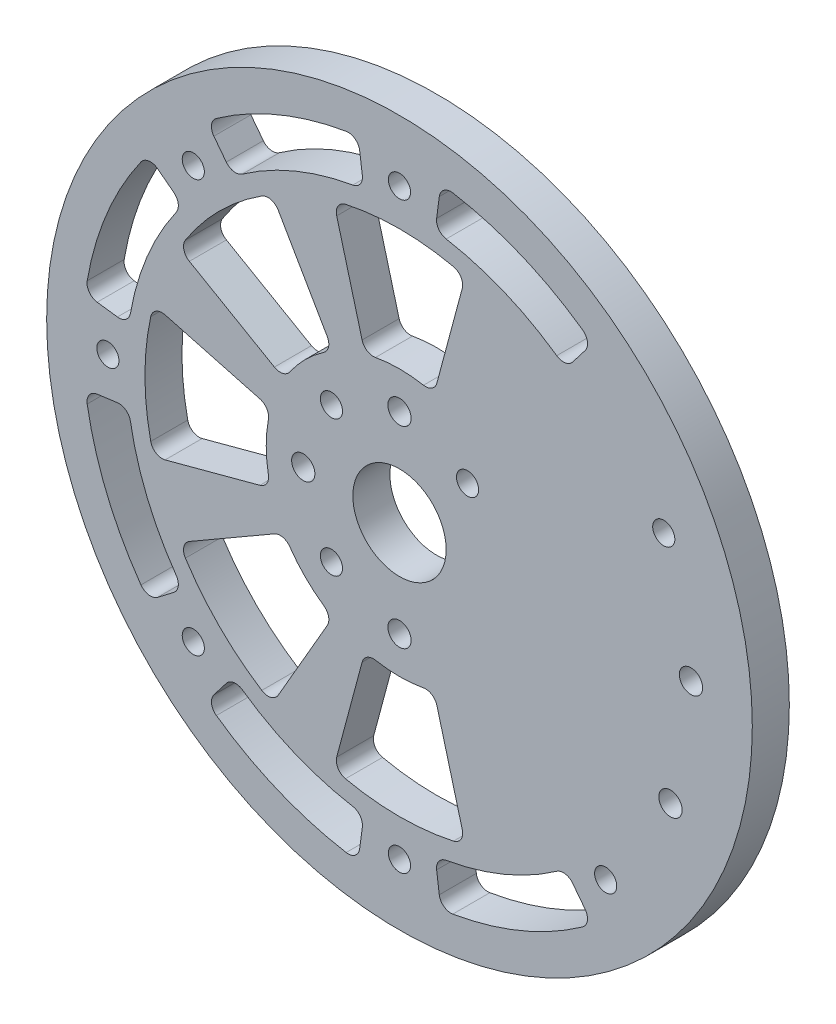
SolidWorks part; units mm, degrees
material "Balsa"
ref_plane "Front Plane" through (0, 0, 0) normal (0, 0, 1) x (1, 0, 0)
ref_plane "Top Plane" through (0, 0, 0) normal (0, 1, 0) x (1, 0, 0)
ref_plane "Right Plane" through (0, 0, 0) normal (1, 0, 0) x (0, 0, -1)
sketch "Sketch1" plane through (0, 0, 0) normal (0, 0, 1) x (1, 0, 0)
  line L0 (45.3154, 21.1309) -> (0, 0) construction
  line L1 (0, 0) -> (35.3553, -35.3553) construction
  line L2 (49.9788, 1.4542) -> (0, 0) construction
  line L3 (0, 0) -> (46.4674, -18.4603) construction
  circle A0 centre (45.3154, 21.1309) radius 1.8986
  circle A1 centre (49.9788, 1.4542) radius 1.9939
  circle A2 centre (0, 0) radius 60.5
  circle A3 centre (0, 0) radius 8
  circle A4 centre (0, 0) radius 16.5 construction
  circle A5 centre (46.4674, -18.4603) radius 1.9939
  circle A6 centre (0, 0) radius 50 construction
  circle A27 centre (0, -16.5) radius 1.9939
  circle A28 centre (11.6673, -11.6673) radius 1.8986 construction
  circle A30 centre (0, -50) radius 1.8986
  circle A31 centre (-16.5, 0) radius 1.9939
  circle A32 centre (-11.6673, -11.6673) radius 1.8986
  circle A33 centre (0, 16.5) radius 1.9939
  circle A34 centre (-11.6673, 11.6673) radius 1.8986
  circle A35 centre (16.5, 0) radius 1.9939 construction
  circle A36 centre (11.6673, 11.6673) radius 1.8986
  circle A38 centre (-35.3553, -35.3553) radius 1.8986
  circle A40 centre (-50, 0) radius 1.8986
  circle A42 centre (-35.3553, 35.3553) radius 1.8986
  circle A44 centre (0, 50) radius 1.8986
  circle A46 centre (35.3553, 35.3553) radius 1.8986 construction
  circle A48 centre (50, 0) radius 1.8986 construction
  circle A50 centre (35.3553, -35.3553) radius 1.8986
  dimension "D1" = 121
  dimension "D4" = 70
  dimension "D6" = 100
  dimension "D7" = 23.333
  dimension "D8" = 33
  dimension "D9" = 3.7973
  dimension "D10" = 3.9878
  dimension "D15" = 3.7973
  dimension "D17" = 3.9878
  dimension "D18" = 3.7973
  dimension "D3" = 16
  dimension "D11" = 3.9878
  dimension "D5" = 23.333
  dimension "D19" = 45
  dimension "D20" = 4
  dimension "D21" = 8
extrude "Boss-Extrude1" add sketch "Sketch1" along normal blind 6.35
sketch "Sketch2" plane through (0, 0, 6.35) normal (0, 0, 1) x (1, 0, 0)
  line L0 (0, 0) -> (-83.0843, 0) construction
  line L1 (-22.0714, 5.914) -> (-42.1627, 11.2975)
  line L2 (-22.0714, -5.914) -> (-42.1627, -11.2975)
  arc A0 (-42.1627, -11.2975) -> (-42.1627, 11.2975) centre (0, 0) cw
  arc A1 (-22.0714, -5.914) -> (-22.0714, 5.914) centre (0, 0) cw
  circle A2 centre (-16.5, 0) radius 1.9939 construction
  circle A3 centre (-50, 0) radius 1.8987 construction
  point P7 (-22.85, 0)
  point P10 (-43.65, 0)
  dimension "D2" = 6.35
  dimension "D3" = 6.35
  dimension "D1" = 30
extrude "Cut-Extrude1" cut sketch "Sketch2" against normal through all
fillet "Fillet1" radius 2 4 edges at (-42.1627, -11.2975, 3.175) (-22.0714, -5.914, 3.175) (-22.0714, 5.914, 3.175) (-42.1627, 11.2975, 3.175)
pattern_circular "CirPattern1" count 8 over 360 about axis through (0, 0, 0) along (0, 0, 1) skipping 3, 4, 5 of "Fillet1", "Cut-Extrude1"
sketch "Sketch3" plane through (0, 0, 6.35) normal (0, 0, 1) x (1, 0, 0)
  line L0 (-83.2273, 0) -> (0, 0) construction
  line L1 (0, 0) -> (-85.2421, 35.3084) construction
  line L2 (-43.0989, 33.071) -> (-37.1488, 28.5053)
  line L3 (-46.4244, 6.1119) -> (-53.8602, 7.0908)
  arc A0 (-53.8602, 7.0908) -> (-43.0989, 33.071) centre (0, 0) cw
  arc A1 (-46.4244, 6.1119) -> (-37.1488, 28.5053) centre (0, 0) cw
  circle A2 centre (-50, 0) radius 1.8987 construction
  circle A3 centre (-50, 0) radius 1.8986 construction
  circle A4 centre (0, 0) radius 60.5 construction
  arc A5 (-42.6565, 9.2598) -> (-42.6565, -9.2598) centre (0, 0) ccw construction
  point P12 (-43.2607, 17.9192)
  dimension "D3" = 6.175
  dimension "D4" = 3.175
  dimension "D1" = 22.5
  dimension "D2" = 30
extrude "Cut-Extrude2" cut sketch "Sketch3" against normal through all
fillet "Fillet2" radius 2 4 edges at (-53.8602, 7.0908, 3.175) (-46.4244, 6.1119, 3.175) (-37.1488, 28.5053, 3.175) (-43.0989, 33.071, 3.175)
pattern_circular "CirPattern3" count 8 over 360 about axis through (0, 0, 0) along (0, 0, 1) skipping 3, 4 of "Cut-Extrude2", "Fillet2"
sketch "Sketch4" plane through (0, 0, 0) normal (0, 0, -1) x (-1, 0, 0)
  circle A0 centre (0, 50) radius 1.8986 construction
  circle A1 centre (35.3553, 35.3553) radius 1.8987 construction
  circle A2 centre (50, 0) radius 1.8987 construction
  circle A3 centre (35.3553, -35.3553) radius 1.8987 construction
  circle A4 centre (0, -50) radius 1.8986 construction
  circle A5 centre (-35.3553, -35.3553) radius 1.8987 construction
  circle A6 centre (-45.3154, 21.1309) radius 1.8987 construction
  circle A7 centre (0, 50) radius 1.8986
  circle A8 centre (35.3553, 35.3553) radius 1.8986
  circle A9 centre (50, 0) radius 1.8986
  circle A10 centre (35.3553, -35.3553) radius 1.8986
  circle A11 centre (0, -50) radius 1.8986
  circle A12 centre (-35.3553, -35.3553) radius 1.8986
  circle A13 centre (-45.3154, 21.1309) radius 1.8986
  circle A14 centre (0, 50) radius 4.7625
  circle A15 centre (35.3553, 35.3553) radius 4.7625
  circle A16 centre (50, 0) radius 4.7625
  circle A17 centre (35.3553, -35.3553) radius 4.7625
  circle A18 centre (0, -50) radius 4.7625
  circle A19 centre (-35.3553, -35.3553) radius 4.7625
  circle A20 centre (-45.3154, 21.1309) radius 4.7625
  dimension "D1" = 9.525
extrude "Cut-Extrude3" cut sketch "Sketch4" against normal blind 3.5719
